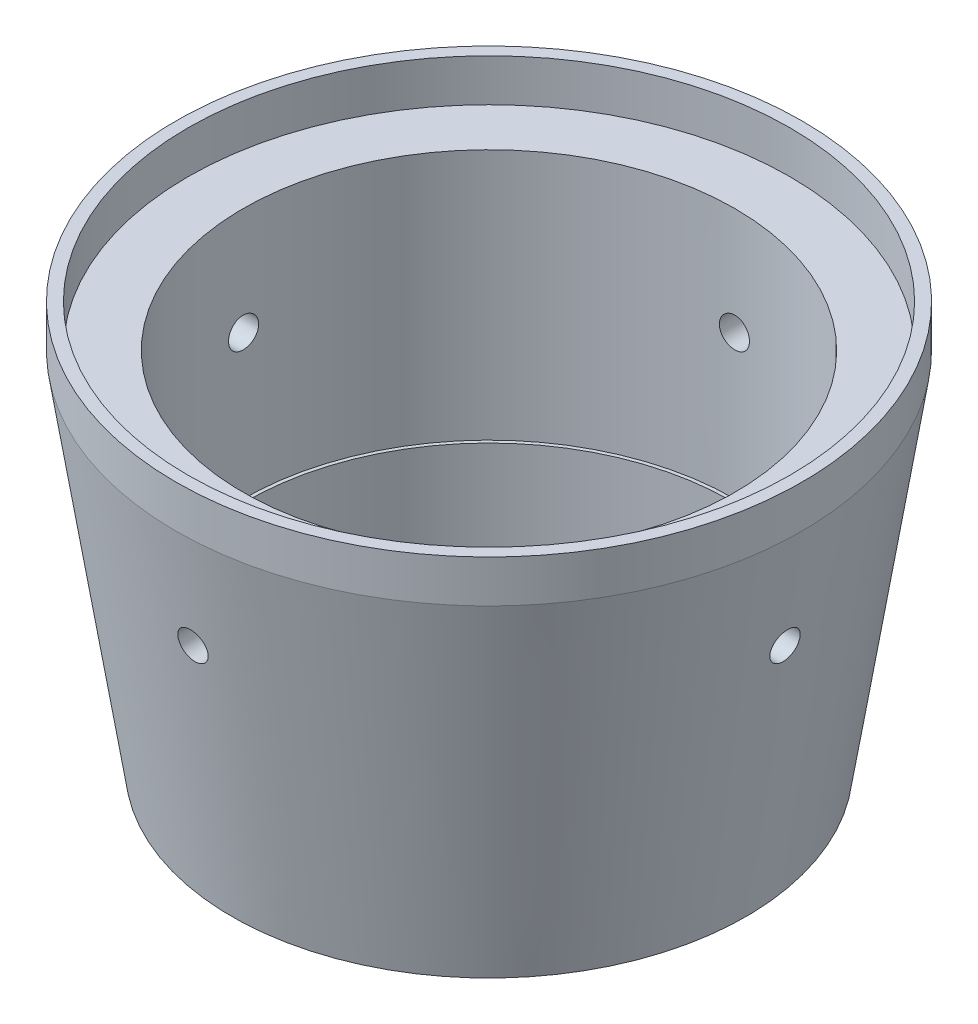
SolidWorks part; units mm, degrees
ref_plane "Front Plane" through (0, 0, 0) normal (0, 0, 1) x (1, 0, 0)
ref_plane "Top Plane" through (0, 0, 0) normal (0, 1, 0) x (1, 0, 0)
ref_plane "Right Plane" through (0, 0, 0) normal (1, 0, 0) x (0, 0, -1)
sketch "Sketch1" plane through (0, 0, 0) normal (0, 0, 1) x (1, 0, 0)
  line L0 (28.1305, 36.322) -> (28.1305, 32.512)
  line L1 (28.1305, 32.512) -> (23.114, 0)
  line L2 (23.114, 0) -> (22.098, 0)
  line L3 (22.098, 0) -> (22.098, 32.512)
  line L4 (22.098, 32.512) -> (27.051, 32.512)
  line L5 (27.051, 32.512) -> (27.051, 36.322)
  line L6 (27.051, 36.322) -> (28.1305, 36.322)
  dimension "D1" = 28.1305
  dimension "D2" = 22.098
  dimension "D3" = 32.512
  dimension "D4" = 3.81
  dimension "D5" = 27.051
  dimension "D6" = 1.016
ref_axis "Axis1" through (0, -2.3241, 0) along (0, 1, 0)
revolve "Revolve1" add sketch "Sketch1" angle 360 about axis through (0, -2.3241, 0) along (0, 1, 0)
ref_plane "Plane1" through (0, 0, 28.1305) normal (0, 0, 1) x (1, 0, 0)
sketch "Sketch4" plane through (0, 0, 28.1305) normal (0, 0, 1) x (1, 0, 0)
  line L0 (0, -2.3241) -> (0, 48.8061) construction
  line L1 (-23.114, 0) -> (23.114, 0) construction
  point P0 (0, 22.86)
  dimension "D1" = 22.86
hole_wizard "#6-32 Tapped Hole1" positions "Sketch4" profile "Sketch5" tap size "#6-32" standard "ANSI Inch"
sketch "Sketch5" plane through (0, 22.86, 28.1305) normal (1, 0, 0) x (0, -1, 0)
  line L0 (0, 0) -> (0, 6.0325)
  line L1 (0, 6.0325) -> (1.3525, 6.0325)
  line L2 (1.3525, 6.0325) -> (1.3525, 0)
  line L5 (1.3525, 0) -> (0, 0)
  line L11 (0, -6.35) -> (0, 107.95) construction
  dimension "Thru Tap Drill Dia." = 2.7051
  dimension "Thru Tap Drill Depth" = 6.0325
cosmetic thread "Hole Thread7" parameters "D2"=3.5052
pattern_circular "CirPattern2" count 4 over 360 about axis through (0, 0, 0) along (0, 1, 0) of "#6-32 Tapped Hole1"
cosmetic thread "Hole Thread8" parameters "D2"=3.5052
cosmetic thread "Hole Thread9" parameters "D2"=3.5052
cosmetic thread "Hole Thread10" parameters "D2"=3.5052
sketch "Sketch6" plane through (0, 0, 0) normal (0, -1, 0) x (1, 0, 0)
  circle A0 centre (0, 0) radius 21.7805
  circle A1 centre (0, 0) radius 22.098 construction
  circle A2 centre (0, 0) radius 22.098
  dimension "D1" = 43.561
extrude "Boss-Extrude1" add sketch "Sketch6" against normal blind 9.906
